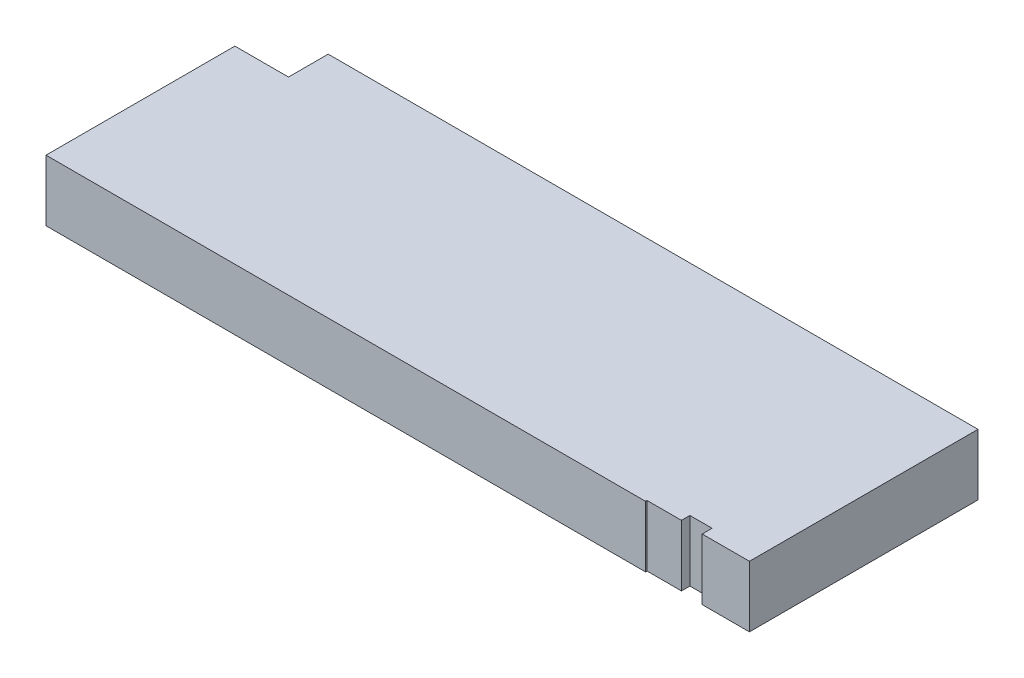
SolidWorks part; units mm, degrees
ref_plane "Front Plane" through (0, 0, 0) normal (0, 0, 1) x (1, 0, 0)
ref_plane "Top Plane" through (0, 0, 0) normal (0, 1, 0) x (1, 0, 0)
ref_plane "Right Plane" through (0, 0, 0) normal (1, 0, 0) x (0, 0, -1)
sketch "Sketch1" plane through (0, 0, 0) normal (0, 1, 0) x (1, 0, 0)
  line L0 (0, 0) -> (0, 44.75)
  line L1 (0, 44.75) -> (12.7, 44.75)
  line L2 (12.7, 44.75) -> (12.7, 54.15)
  line L3 (12.7, 54.15) -> (166.65, 54.15)
  line L6 (166.65, 54.15) -> (166.65, 0)
  line L7 (166.65, 0) -> (155.45, 0)
  line L8 (155.45, 0) -> (155.45, 2.35)
  line L9 (155.45, 2.35) -> (150.2, 2.35)
  line L10 (150.2, 2.35) -> (150.2, 0.35)
  line L11 (150.2, 0.35) -> (142.05, 0.35)
  line L12 (142.05, 0.35) -> (142.05, 0)
  line L13 (142.05, 0) -> (0, 0)
  dimension "D1" = 9.4
  dimension "D2" = 166.65
  dimension "D3" = 2.35
  dimension "D4" = 5.25
  dimension "D5" = 13.4
  dimension "D6" = 0.35
  dimension "D7" = 142.05
  dimension "D8" = 54.15
  dimension "D9" = 12.7
extrude "Boss-Extrude1" add sketch "Sketch1" along normal blind 14.49
